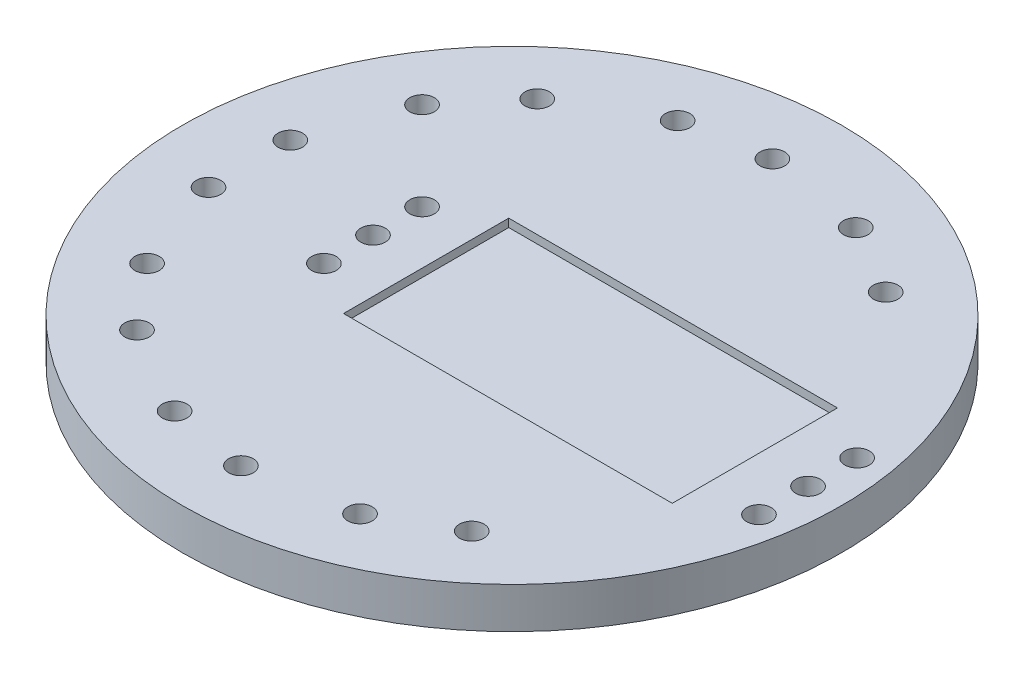
SolidWorks part; units mm, degrees
ref_plane "Front Plane" through (0, 0, 0) normal (0, 0, 1) x (1, 0, 0)
ref_plane "Top Plane" through (0, 0, 0) normal (0, 1, 0) x (1, 0, 0)
ref_plane "Right Plane" through (0, 0, 0) normal (1, 0, 0) x (0, 0, -1)
sketch "Sketch1" plane through (0, 0, 0) normal (0, 1, 0) x (1, 0, 0)
  line L0 (0, 40.3) -> (0, 0) construction
  circle A0 centre (0, 0) radius 40.3
  point P55 (0, 0)
  dimension "D1" = 80.6
extrude "Boss-Extrude1" add sketch "Sketch1" along normal blind 5
sketch "Sketch2" plane through (0, 5, 0) normal (0, 1, 0) x (1, 0, 0)
  line L1 (29.7, -10.1) -> (-10.5, -10.1)
  line L2 (29.7, -10.1) -> (29.7, 10.1)
  line L3 (29.7, 10.1) -> (-10.5, 10.1)
  line L4 (-10.5, -10.1) -> (-10.5, 10.1)
  line L5 (29.7, -10.1) -> (-10.5, 10.1) construction
  line L6 (29.7, 10.1) -> (-10.5, -10.1) construction
  point P0 (9.6, 0)
  dimension "D1" = 10.5
  dimension "D2" = 40.2
  dimension "D3" = 20.2
extrude "Cut-Extrude3" cut sketch "Sketch2" against normal blind 1
sketch "Sketch3" plane through (0, 5, 0) normal (0, 1, 0) x (1, 0, 0)
  line L0 (-10.5, 10.1) -> (-10.5, -10.1) construction
  line L1 (29.7, -10.1) -> (29.7, 10.1) construction
  circle A0 centre (-17, -6) radius 1.5
  circle A1 centre (-17, 0) radius 1.5
  circle A2 centre (-17, 6) radius 1.5
  circle A3 centre (36.2, -6) radius 1.5
  circle A4 centre (36.2, 0) radius 1.5
  circle A5 centre (36.2, 6) radius 1.5
  dimension "D1" = 3
  dimension "D3" = 3
  dimension "D4" = 3
  dimension "D5" = 6
  dimension "D7" = 3
  dimension "D8" = 3
  dimension "D9" = 3
  dimension "D2" = 6.5
  dimension "D6" = 6
  dimension "D10" = 6
  dimension "D11" = 6
  dimension "D12" = 6.5
extrude "Cut-Extrude4" cut sketch "Sketch3" against normal through all
sketch "Sketch4" plane through (0, 5, 0) normal (0, 1, 0) x (1, 0, 0)
  line L0 (-32.1131, 5) -> (-32.1131, -5) construction
  circle A0 centre (-32.1131, 5) radius 1.5
  circle A1 centre (-32.1131, -5) radius 1.5
  circle A2 centre (0, 0) radius 32.5 construction
  point P5 (-32.1131, 0)
  point P8 (0, 0)
  dimension "D1" = 3
  dimension "D2" = 3
  dimension "D3" = 65
  dimension "D4" = 10
extrude "Cut-Extrude5" cut sketch "Sketch4" against normal up to next
sketch "Sketch5" plane through (0, 5, 0) normal (0, 1, 0) x (1, 0, 0)
  circle A0 centre (-32.1131, 5) radius 1.5 construction
  circle A1 centre (-32.1131, 5) radius 1.5
  circle A2 centre (-32.1131, -5) radius 1.5 construction
  circle A3 centre (-32.1131, -5) radius 1.5
  circle A4 centre (-21.3861, 24.4721) radius 1.5
  circle A5 centre (-27.814, 16.8117) radius 1.5
  circle A6 centre (-0.6523, 32.4935) radius 1.5
  circle A7 centre (-10.5004, 30.757) radius 1.5
  circle A8 centre (20.3867, 25.3107) radius 1.5
  circle A9 centre (11.7264, 30.3107) radius 1.5
  circle A10 centre (-27.814, -16.8117) radius 1.5
  circle A11 centre (-21.3861, -24.4721) radius 1.5
  circle A12 centre (-10.5004, -30.757) radius 1.5
  circle A13 centre (-0.6523, -32.4935) radius 1.5
  circle A14 centre (11.7264, -30.3107) radius 1.5
  circle A15 centre (20.3867, -25.3107) radius 1.5
  point P20 (0, 0)
  point P33 (0, 0)
  dimension "D1" = 4
  dimension "D2" = 4
extrude "Cut-Extrude6" cut sketch "Sketch5" against normal through all
